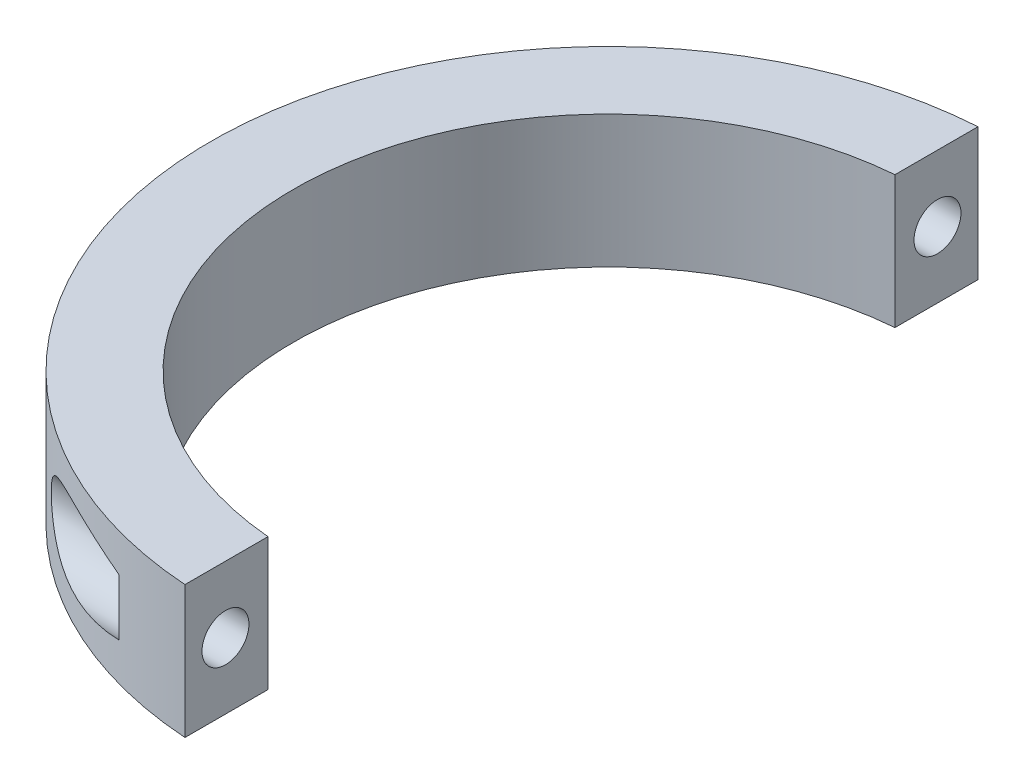
SolidWorks part; units mm, degrees
material "1060 Alloy"
ref_plane "Front Plane" through (0, 0, 0) normal (0, 0, 1) x (1, 0, 0)
ref_plane "Top Plane" through (0, 0, 0) normal (0, 1, 0) x (1, 0, 0)
ref_plane "Right Plane" through (0, 0, 0) normal (1, 0, 0) x (0, 0, -1)
sketch "Sketch1" plane through (0, 0, 0) normal (0, 1, 0) x (1, 0, 0)
  line L0 (0, 30.1625) -> (0, -30.1625) construction
  line L1 (0, 30.1625) -> (0, 38.1)
  line L2 (0, -30.1625) -> (0, -38.1)
  arc A0 (0, 30.1625) -> (0, -30.1625) centre (0, 0) ccw
  arc A1 (0, 38.1) -> (0, -38.1) centre (0, 0) ccw
  dimension "D1" = 30.1625
  dimension "D2" = 38.1
extrude "Boss-Extrude1" add sketch "Sketch1" along normal blind 12.7 contours A1 L2 A0 L1
sketch "Sketch2" plane through (0, 0, 0) normal (1, 0, 0) x (0, 0, -1)
  line L0 (-30.1625, 0) -> (-38.1, 12.7) construction
  line L1 (30.1625, 0) -> (38.1, 12.7) construction
  circle A0 centre (-34.1313, 6.35) radius 2.25
  circle A1 centre (34.1313, 6.35) radius 2.25
  point P6 (-34.1313, 6.35)
  dimension "D1" = 4.5
extrude "Cut-Extrude1" cut sketch "Sketch2" against normal through all
sketch "Sketch3" plane through (0, 0, 0) normal (1, 0, 0) x (0, 0, -1)
  circle A0 centre (34.1313, 6.35) radius 3.75
  circle A1 centre (-34.1313, 6.35) radius 3.75
  dimension "D1" = 7.5
extrude "Cut-Extrude2" cut sketch "Sketch3" against normal through all from offset 10.16 offset against normal yes
sketch "Sketch4" plane through (0, 12.7, 0) normal (0, 1, 0) x (1, 0, 0)
  line L1 (0, 38.1) -> (-2.54, 38.1)
  line L2 (0, 38.1) -> (0, -38.1)
  line L3 (0, -38.1) -> (-2.54, -38.1)
  line L4 (-2.54, 38.1) -> (-2.54, -38.1)
  dimension "D1" = 2.54
extrude "Cut-Extrude3" cut sketch "Sketch4" against normal through all contours L4 L3 L2 L1
